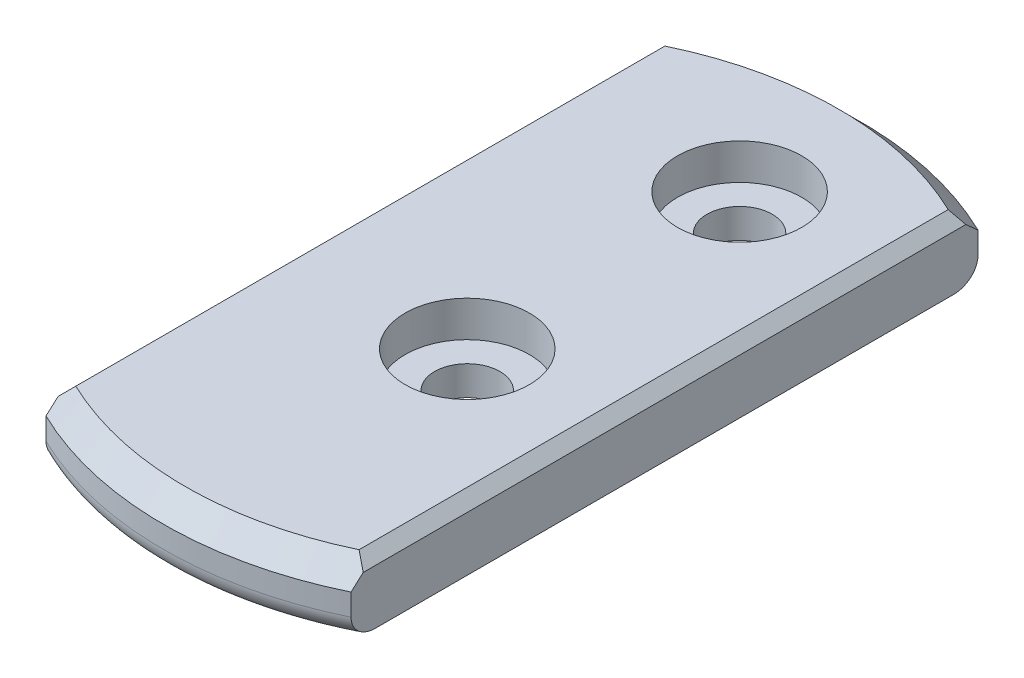
SolidWorks part; units mm, degrees
ref_plane "Front Plane" through (0, 0, 0) normal (0, 0, 1) x (1, 0, 0)
ref_plane "Top Plane" through (0, 0, 0) normal (0, 1, 0) x (1, 0, 0)
ref_plane "Right Plane" through (0, 0, 0) normal (1, 0, 0) x (0, 0, -1)
sketch "Sketch2" plane through (0, 0, 0) normal (0, 1, 0) x (1, 0, 0)
  circle A0 centre (0, 0) radius 16
  dimension "D1" = 32
extrude "Boss-Extrude1" add sketch "Sketch2" along normal blind 3
sketch "Sketch1" plane through (0, 0, 0) normal (0, 1, 0) x (1, 0, 0)
  line L1 (-16, 16) -> (-7, 16)
  line L2 (-16, 16) -> (-16, -16)
  line L3 (-16, -16) -> (-7, -16)
  line L4 (-7, 16) -> (-7, -16)
  line L5 (16, 16) -> (7, 16)
  line L6 (16, 16) -> (16, -16)
  line L7 (16, -16) -> (7, -16)
  line L8 (7, 16) -> (7, -16)
  circle A0 centre (0, 0) radius 16 construction
  dimension "D1" = 32
  dimension "D2" = 7
extrude "Cut-Extrude1" cut sketch "Sketch1" along normal through all
sketch "Sketch3" plane through (0, 3, 0) normal (0, 1, 0) x (1, 0, 0)
  line L0 (7, 14.3875) -> (7, -14.3875) construction
  circle A0 centre (1, 9.4472) radius 1.5
  circle A1 centre (1, -3.0528) radius 1.5
  dimension "D4" = 3
  dimension "D1" = 6
  dimension "D2" = 9.4472
  dimension "D3" = 12.5
extrude "Cut-Extrude2" cut sketch "Sketch3" against normal through all
sketch "Sketch4" plane through (0, 3, 0) normal (0, 1, 0) x (1, 0, 0)
  circle A0 centre (1, 9.4472) radius 2.85
  circle A1 centre (1, -3.0528) radius 2.85
  dimension "D1" = 5.7
extrude "Cut-Extrude3" cut sketch "Sketch4" against normal blind 1.65
chamfer "Chamfer1" distance 0.5 angle 45 2 edges at (-7, 3, 0) (7, 3, 0)
fillet "Fillet1" radius 1 2 edges at (0, 0, -16) (0, 0, 16)
chamfer "Chamfer2" distance 1 angle 45 2 edges at (0, 3, -16) (0, 3, 16)
